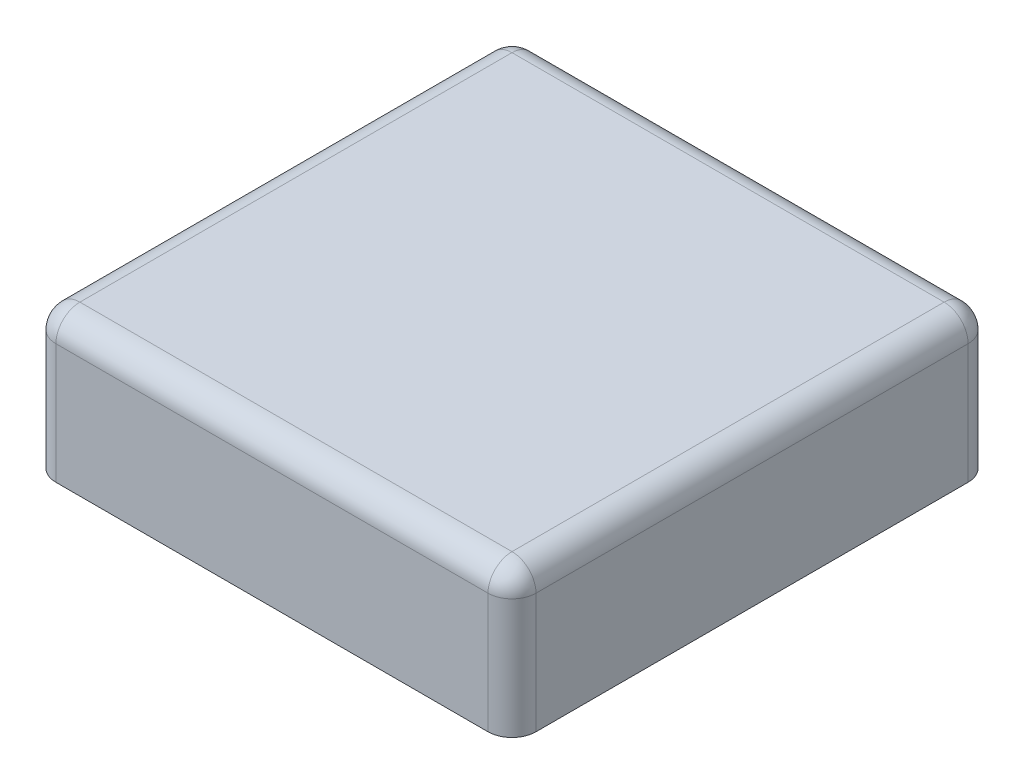
SolidWorks part; units mm, degrees
ref_plane "Front Plane" through (0, 0, 0) normal (0, 0, 1) x (1, 0, 0)
ref_plane "Top Plane" through (0, 0, 0) normal (0, 1, 0) x (1, 0, 0)
ref_plane "Right Plane" through (0, 0, 0) normal (1, 0, 0) x (0, 0, -1)
sketch "Sketch1" plane through (0, 0, 0) normal (0, 1, 0) x (1, 0, 0)
  line L1 (-5, 5) -> (5, 5)
  line L2 (-5, 5) -> (-5, -5)
  line L3 (-5, -5) -> (5, -5)
  line L4 (5, 5) -> (5, -5)
  line L5 (-5, 5) -> (5, -5) construction
  line L6 (-5, -5) -> (5, 5) construction
  point P0 (0, 0)
  dimension "D1" = 10
  dimension "D2" = 10
extrude "Boss-Extrude2" add sketch "Sketch1" against normal blind 3
shell "Shell2" thickness 0.7
fillet "Fillet2" radius 0.5 8 edges at (0, 0, 5) (-5, 0, 0) (0, 0, -5) (5, 0, 0) (-5, -1.5, -5) (5, -1.5, -5) (5, -1.5, 5) (-5, -1.5, 5)
sketch "Sketch5" plane through (0, 0, 0) normal (1, 0, 0) x (0, 0, -1)
  line L0 (3, -0.5) -> (3, -4.5)
  line L1 (4.5, -0.5) -> (-4.5, -0.5) construction
  line L2 (3, -4.5) -> (2.2, -4.5)
  line L3 (2.2, -4.5) -> (1.6836, -3.6056)
  line L4 (1.6836, -3.6056) -> (2.2, -2.7113)
  line L5 (2.2, -2.7113) -> (2.2, -0.5)
  line L6 (2.2, -0.5) -> (3, -0.5)
  line L7 (2.2, -2.7113) -> (2.2, -5.4101) construction
  line L8 (4.5, -3) -> (4.5, -0.5) construction
  line L9 (0, 0) -> (0, -5.7634) construction
  line L10 (-2.2, -2.7113) -> (-2.2, -5.4101) construction
  line L11 (-2.2, -0.5) -> (-3, -0.5)
  line L12 (-2.2, -2.7113) -> (-2.2, -0.5)
  line L13 (-1.6836, -3.6056) -> (-2.2, -2.7113)
  line L14 (-2.2, -4.5) -> (-1.6836, -3.6056)
  line L15 (-3, -4.5) -> (-2.2, -4.5)
  line L16 (-3, -0.5) -> (-3, -4.5)
  dimension "D1" = 150
  dimension "D2" = 150
  dimension "D3" = 0.8
  dimension "D4" = 1.5
  dimension "D5" = 4
extrude "Boss-Extrude3" add sketch "Sketch5" against normal mid plane 5 separate body
sketch "Sketch6" plane through (0, 0, 0) normal (0, 0, 1) x (1, 0, 0)
  line L0 (2.7, -0.5) -> (2.7, -4.3)
  line L1 (4.5, -0.5) -> (-4.5, -0.5) construction
  line L2 (2.7, -4.3) -> (1.9, -4.3)
  line L3 (1.9, -4.3) -> (1.9, -0.5)
  line L4 (1.9, -0.5) -> (2.7, -0.5)
  line L5 (4.5, -3) -> (4.5, -0.5) construction
  line L6 (0, 0) -> (0, -50000) construction
  line L7 (-1.9, -0.5) -> (-2.7, -0.5)
  line L8 (-1.9, -4.3) -> (-1.9, -0.5)
  line L9 (-2.7, -4.3) -> (-1.9, -4.3)
  line L10 (-2.7, -0.5) -> (-2.7, -4.3)
  dimension "D1" = 0.8
  dimension "D2" = 1.8
  dimension "D3" = 3.8
extrude "Boss-Extrude4" add sketch "Sketch6" along normal mid plane 2
sketch "Sketch7" plane through (0, 0, 0) normal (1, 0, 0) x (0, 0, -1)
  line L0 (-4.5, -0.5) -> (-3, -0.5)
  line L1 (4.5, -0.5) -> (-4.5, -0.5) construction
  line L2 (-3, -0.5) -> (-3, -4.5) construction
  line L3 (-3, -0.5) -> (-3, -2.7)
  line L4 (-3, -2.7) -> (-4.5, -2.7)
  line L5 (-4.5, -0.5) -> (-4.5, -3) construction
  line L6 (-4.5, -2.7) -> (-4.5, -0.5)
  line L7 (0, 0) -> (0, -50000) construction
  line L8 (4.5, -2.7) -> (4.5, -0.5)
  line L9 (3, -2.7) -> (4.5, -2.7)
  line L10 (3, -0.5) -> (3, -2.7)
  line L11 (4.5, -0.5) -> (3, -0.5)
  dimension "D1" = 2.2
extrude "Boss-Extrude5" add sketch "Sketch7" along normal mid plane 0.7
sketch "Sketch9" plane through (0, 0, 0) normal (0, 0, 1) x (1, 0, 0)
  line L0 (-4.5, -2.7) -> (-2.7, -2.7)
  line L1 (-4.5, -0.5) -> (-4.5, -3) construction
  line L2 (-2.7, -0.7) -> (-2.7, -4.3) construction
  line L3 (-2.7, -2.7) -> (-2.7, -0.5)
  line L4 (4.5, -0.5) -> (-4.5, -0.5) construction
  line L5 (-2.7, -0.5) -> (-4.5, -0.5)
  line L6 (-4.5, -0.5) -> (-4.5, -2.7)
  line L7 (0, -1000) -> (0, 49000) construction
  line L8 (4.5, -0.5) -> (4.5, -2.7)
  line L9 (2.7, -0.5) -> (4.5, -0.5)
  line L10 (2.7, -2.7) -> (2.7, -0.5)
  line L11 (4.5, -2.7) -> (2.7, -2.7)
  dimension "D1" = 2.2
extrude "Boss-Extrude6" add sketch "Sketch9" along normal mid plane 0.7
